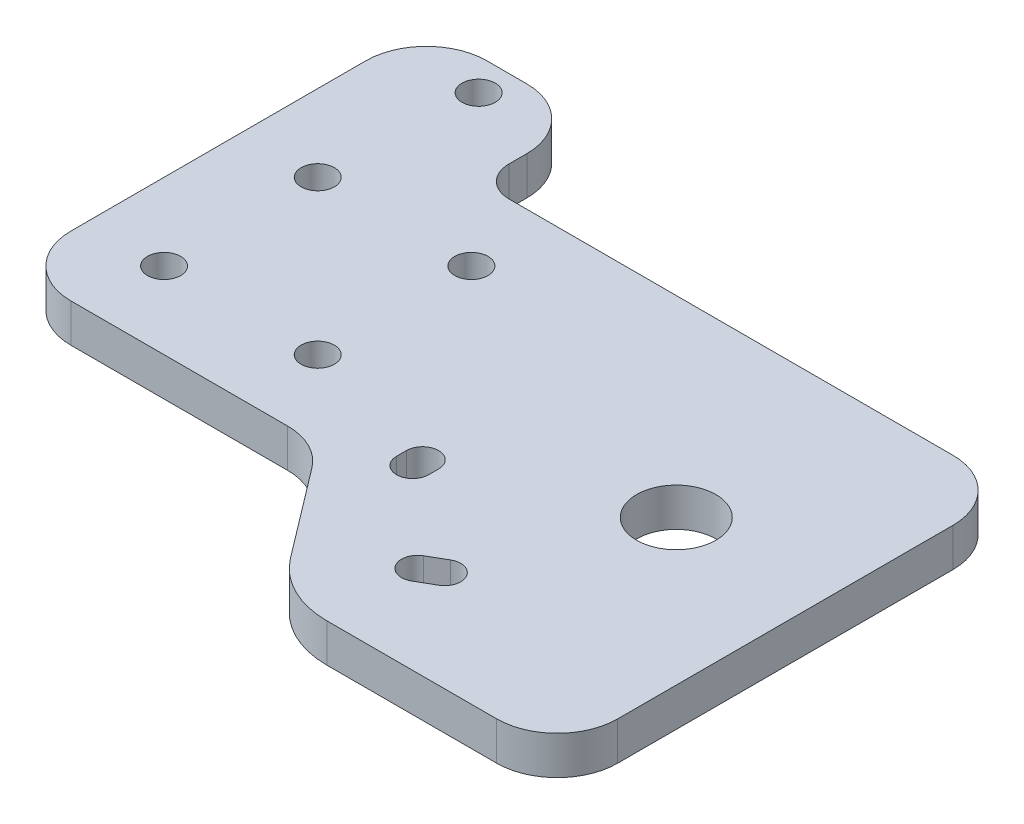
SolidWorks part; units mm, degrees
material "6061-T6 (SS)"
ref_plane "Front" through (0, 0, 0) normal (0, 0, 1) x (1, 0, 0)
ref_plane "Top" through (0, 0, 0) normal (0, 1, 0) x (1, 0, 0)
ref_plane "Right" through (0, 0, 0) normal (1, 0, 0) x (0, 0, -1)
sketch "Sketch1" plane through (0, 0, 0) normal (0, 1, 0) x (1, 0, 0)
  line L0 (0, 0) -> (89.6212, 0) construction
  line L1 (25.4, -25.4) -> (-25.4, -25.4)
  line L2 (25.4, -25.4) -> (25.4, 25.4) construction
  line L3 (25.4, 25.4) -> (-25.4, 25.4) construction
  line L4 (-25.4, -25.4) -> (-25.4, 25.4)
  line L5 (25.4, -25.4) -> (-25.4, 25.4) construction
  line L6 (25.4, 25.4) -> (-25.4, -25.4) construction
  line L7 (1.2, 25.4) -> (1.2, 76.2) construction
  line L8 (-12.7, 25.4) -> (-12.7, -25.4) construction
  line L9 (12.7, -25.4) -> (12.7, 25.4) construction
  line L10 (0, 0) -> (-25.4, 0) construction
  line L11 (-12.7, 0) -> (-12.7, 25.4) construction
  line L12 (-12.7, 12.7) -> (12.7, 12.7) construction
  line L13 (38.1, -41.4) -> (89.6212, -41.4) construction
  line L14 (86.6212, -27.36) -> (44.6212, -27.36) construction
  line L15 (86.6212, -27.36) -> (86.6212, 14.64) construction
  line L16 (86.6212, 14.64) -> (44.6212, 14.64) construction
  line L17 (44.6212, -27.36) -> (44.6212, 14.64) construction
  line L18 (86.6212, -27.36) -> (44.6212, 14.64) construction
  line L19 (86.6212, 14.64) -> (44.6212, -27.36) construction
  line L20 (81.1212, -21.86) -> (50.1212, -21.86) construction
  line L21 (81.1212, -21.86) -> (81.1212, 9.14) construction
  line L22 (81.1212, 9.14) -> (50.1212, 9.14) construction
  line L23 (50.1212, -21.86) -> (50.1212, 9.14) construction
  line L24 (81.1212, -21.86) -> (50.1212, 9.14) construction
  line L25 (81.1212, 9.14) -> (50.1212, -21.86) construction
  line L26 (89.6212, -41.4) -> (89.6212, 0) construction
  line L27 (36.4, -12.72) -> (65.6212, -12.72) construction
  line L28 (35.1664, -25.3192) -> (52.7755, -28.8008) construction
  line L29 (25.4, -25.4) -> (39.5919, -44.1062)
  line L30 (65.6212, 0) -> (0, 0) construction
  line L31 (1.2, 76.2) -> (-49.6, 76.2) construction
  line L32 (51.5419, -50.04) -> (89.6212, -50.04)
  line L33 (89.6212, -50.04) -> (89.6212, 25.4)
  line L34 (89.6212, 25.4) -> (25.4, 25.4)
  line L35 (36.4, -19.08) -> (36.4, -20.72) construction
  line L36 (51.5419, -35.04) -> (54.3783, -33.4) construction
  line L37 (51.5419, -35.04) -> (51.5419, -50.04) construction
  line L38 (-49.6, 76.2) -> (-49.6, 25.4) construction
  line L39 (-49.6, -25.4) -> (-25.4, -25.4) construction
  line L40 (-49.6, 25.4) -> (-25.4, 25.4) construction
  line L41 (-11.5, 25.4) -> (-11.5, 76.2) construction
  line L42 (-25.4, 25.4) -> (-25.4, 43.35)
  line L43 (-25.4, 43.35) -> (1.2, 43.35)
  line L44 (1.2, 43.35) -> (1.2, 25.4)
  line L45 (1.2, 25.4) -> (25.4, 25.4)
  circle A0 centre (-12.7, 12.7) radius 2.5 construction
  circle A1 centre (12.7, 12.7) radius 2.5 construction
  circle A2 centre (-12.7, -12.7) radius 2.5 construction
  circle A3 centre (12.7, -12.7) radius 2.5 construction
  circle A4 centre (65.6212, -6.36) radius 6.36 construction
  circle A5 centre (65.6212, -6.36) radius 11 construction
  circle A6 centre (50.1212, 9.14) radius 1.5 construction
  circle A7 centre (81.1212, 9.14) radius 1.5 construction
  circle A8 centre (81.1212, -21.86) radius 1.5 construction
  circle A9 centre (50.1212, -21.86) radius 1.5 construction
  circle A10 centre (51.5419, -35.04) radius 6.36 construction
  circle A11 centre (51.5419, -35.04) radius 11 construction
  circle A12 centre (36.4, -19.08) radius 6.36 construction
  circle A13 centre (36.4, -19.08) radius 11 construction
  circle A14 centre (50.1212, -21.86) radius 3 construction
  circle A15 centre (-11.5, 38.1) radius 2.5 construction
  circle A16 centre (-11.5, 38.1) radius 5.25 construction
  circle A19 centre (36.4, -19.08) radius 2.5 construction
  circle A20 centre (51.5419, -35.04) radius 2.5 construction
  circle A21 centre (65.6212, -6.36) radius 11 construction
  arc A22 (39.5919, -44.1062) -> (51.5419, -50.04) centre (51.5419, -35.04) ccw
  circle A23 centre (36.4, -20.72) radius 8 construction
  circle A24 centre (36.4, -20.72) radius 11 construction
  circle A25 centre (54.3783, -33.4) radius 8 construction
  circle A26 centre (54.3783, -33.4) radius 11 construction
  point P0 (0, 0)
  dimension "D6" = 5
  dimension "D7" = 12.72
  dimension "D9" = 22
  dimension "D11" = 3
  dimension "D12" = 16
  dimension "D13" = 6
  dimension "D16" = 12.7
  dimension "D17" = 5
  dimension "D18" = 22
  dimension "D20" = 16
  dimension "D21" = 4
  dimension "D23" = 10.5
  dimension "D1" = 50.8
  dimension "D2" = 50.8
  dimension "D3" = 50.8
  dimension "D4" = 12.7
  dimension "D5" = 25.4
  dimension "D8" = 42
  dimension "D10" = 31
  dimension "D14" = 50.8
  dimension "D15" = 24.2
  dimension "D19" = 3
  dimension "D22" = 12.7
extrude "Boss-Extrude1" add sketch "Sketch1" along normal blind 6.35
hole_wizard "M5 Clearance Hole1" positions "Sketch3" profile "Sketch2" hole size "M5" standard "ISO" end condition through all
sketch "Sketch3" plane through (0, 6.35, 0) normal (0, 1, 0) x (1, 0, 0)
  point P0 (-12.7, 12.7)
  point P3 (12.7, 12.7)
  point P6 (12.7, -12.7)
  point P9 (-12.7, -12.7)
  point P15 (-11.5, 38.1)
sketch "Sketch2" plane through (-12.7, 6.35, -12.7) normal (1, 0, 0) x (0, 0, 1)
  line L0 (0, 0) -> (0, 6.35)
  line L1 (0, 6.35) -> (2.75, 6.35)
  line L2 (2.75, 6.35) -> (2.75, 0)
  line L5 (2.75, 0) -> (0, 0)
  line L11 (0, -6.35) -> (0, 107.95) construction
  dimension "Thru Hole Dia." = 5.5
  dimension "Thru Hole Depth" = 6.35
sketch "Sketch7" plane through (0, 6.35, 0) normal (0, 1, 0) x (1, 0, 0)
  line L0 (36.4, -19.08) -> (36.4, -20.72) construction
  line L1 (54.3783, -33.4) -> (51.5419, -35.04) construction
  line L2 (53.0518, -31.1059) -> (50.2155, -32.7459)
  line L3 (33.75, -19.08) -> (33.75, -20.72)
  line L4 (55.7047, -35.6941) -> (52.8684, -37.3341)
  line L5 (39.05, -19.08) -> (39.05, -20.72)
  arc A0 (53.0518, -31.1059) -> (55.7047, -35.6941) centre (54.3783, -33.4) cw
  arc A1 (50.2155, -32.7459) -> (52.8684, -37.3341) centre (51.5419, -35.04) ccw
  arc A2 (33.75, -19.08) -> (39.05, -19.08) centre (36.4, -19.08) cw
  arc A3 (33.75, -20.72) -> (39.05, -20.72) centre (36.4, -20.72) ccw
  dimension "D1" = 2.65
  dimension "D2" = 2.65
extrude "Cut-Extrude2" cut sketch "Sketch7" against normal through all
fillet "Fillet1" radius 10 6 edges at (89.6212, 3.175, 50.04) (89.6212, 3.175, -25.4) (25.4, 3.175, 25.4) (-25.4, 3.175, 25.4) (-25.4, 3.175, -43.35) (1.2, 3.175, -43.35)
sketch "Sketch10" plane through (0, 6.35, 0) normal (0, 1, 0) x (1, 0, 0)
  circle A0 centre (65.6212, -6.36) radius 6.55
  dimension "D1" = 13.1
extrude "Cut-Extrude3" cut sketch "Sketch10" against normal through all
fillet "Fillet2" radius 5 1 edges at (1.2, 3.175, -25.4)
